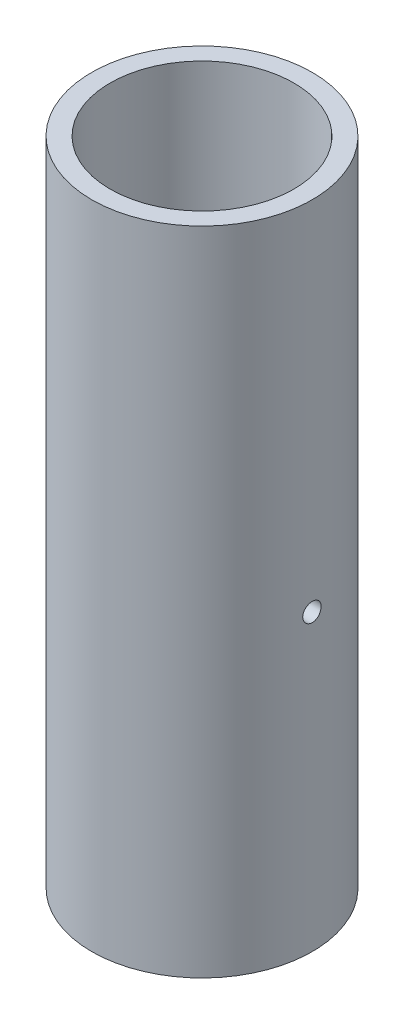
SolidWorks part; units mm, degrees
material "G-10"
ref_plane "Front Plane" through (0, 0, 0) normal (0, 0, 1) x (1, 0, 0)
ref_plane "Top Plane" through (0, 0, 0) normal (0, 1, 0) x (1, 0, 0)
ref_plane "Right Plane" through (0, 0, 0) normal (1, 0, 0) x (0, 0, -1)
sketch "Sketch1" plane through (0, 0, 0) normal (0, 1, 0) x (1, 0, 0)
  circle A0 centre (0, 0) radius 9.525
  circle A1 centre (0, 0) radius 7.9375
  dimension "D1" = 15.875
  dimension "D2" = 19.05
extrude "Extrude1" add sketch "Sketch1" along normal blind 56.23
hole_wizard "1/16 (0.0625) Diameter Hole1" positions "Sketch2" profile "Sketch3" hole size "1/16" standard "ANSI Inch"
sketch "Sketch2" plane through (0, 0, 0) normal (1, 0, 0) x (0, 0, -1)
  point P0 (0, 25.4)
  dimension "D1" = 25.4
sketch "Sketch3" plane through (0, 25.4, 0) normal (0, 1, 0) x (0, 0, 1)
  line L0 (0, 0) -> (0, 10.0019)
  line L1 (0, 10.0019) -> (0.7937, 9.525)
  line L2 (0.7937, 9.525) -> (0.7937, 0)
  line L5 (0.7937, 0) -> (0, 0)
  line L10 (0, 10.0019) -> (-0.7938, 9.525) construction
  line L11 (0, -6.35) -> (0, 107.95) construction
  dimension "Hole Dia." = 1.5875
  dimension "Hole Depth" = 9.525
  dimension "Drill Angle" = 118
